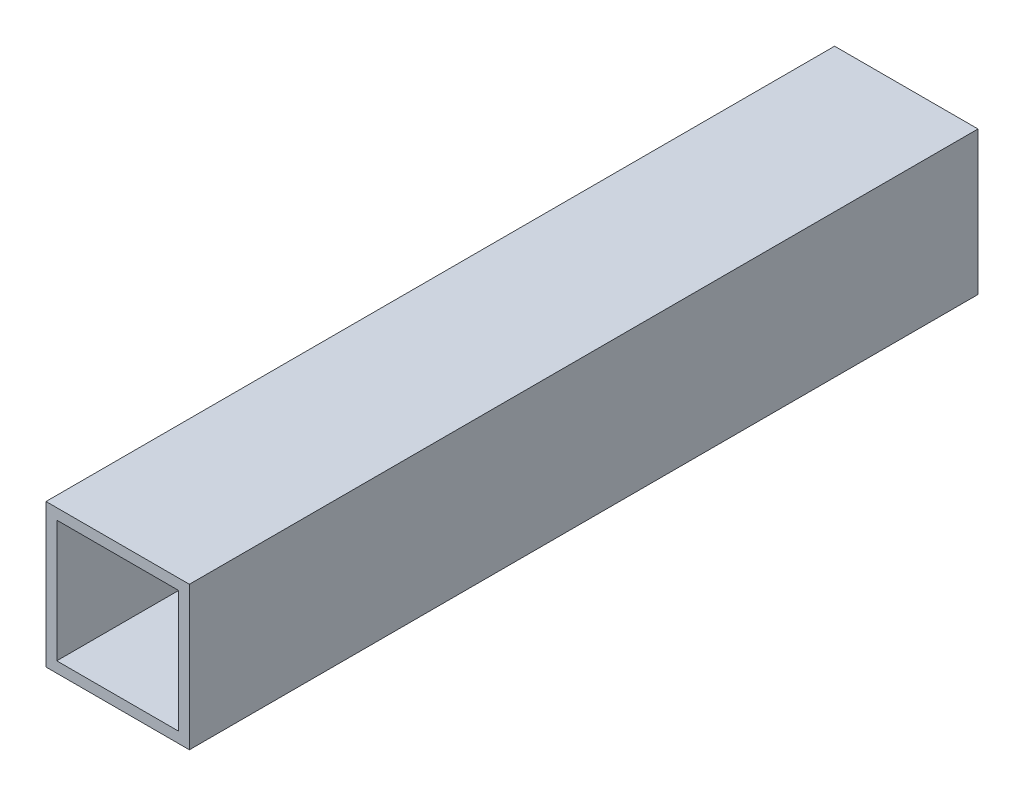
SolidWorks part; units mm, degrees
ref_plane "Front Plane" through (0, 0, 0) normal (0, 0, 1) x (1, 0, 0)
ref_plane "Top Plane" through (0, 0, 0) normal (0, 1, 0) x (1, 0, 0)
ref_plane "Right Plane" through (0, 0, 0) normal (1, 0, 0) x (0, 0, -1)
sketch "Sketch1" plane through (0, 0, 0) normal (0, 0, 1) x (1, 0, 0)
  line L0 (17, 17) -> (-17, 17)
  line L1 (20, -20) -> (-20, -20)
  line L2 (20, -20) -> (20, 20)
  line L3 (20, 20) -> (-20, 20)
  line L4 (-20, -20) -> (-20, 20)
  line L5 (20, -20) -> (-20, 20) construction
  line L6 (20, 20) -> (-20, -20) construction
  line L7 (-17, -17) -> (-17, 17)
  line L8 (17, -17) -> (-17, -17)
  line L9 (17, -17) -> (17, 17)
  point P0 (0, 0)
  dimension "D1" = 40
  dimension "D2" = 3
extrude "Boss-Extrude1" add sketch "Sketch1" along normal blind 220
